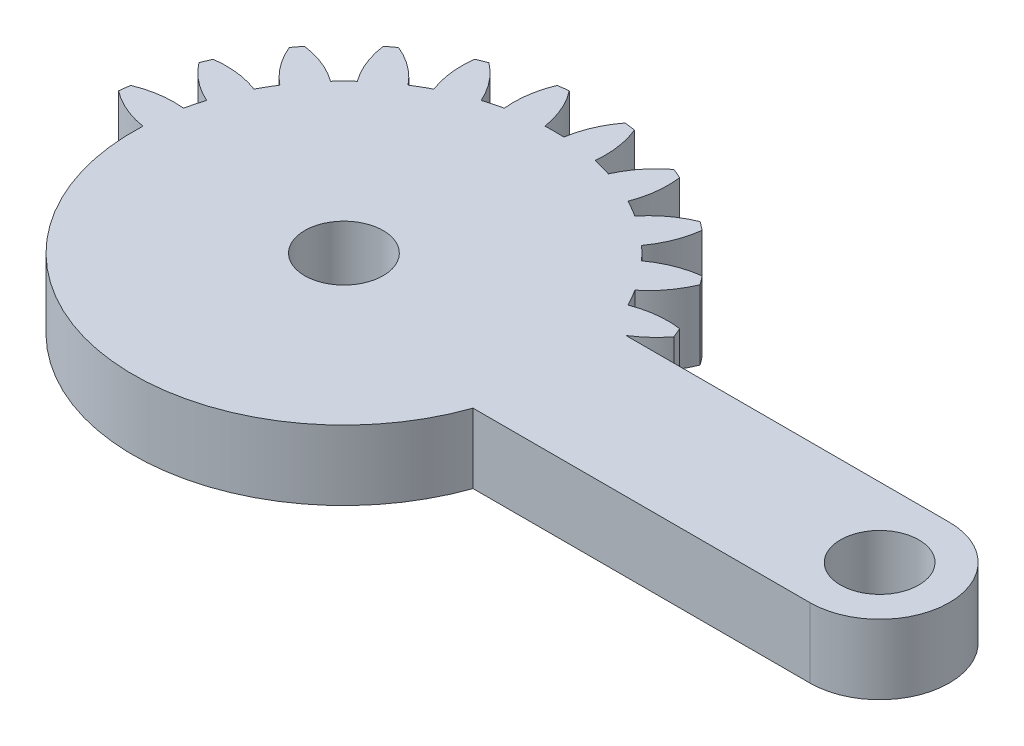
SolidWorks part; units mm, degrees
ref_plane "Front Plane" through (0, 0, 0) normal (0, 0, 1) x (1, 0, 0)
ref_plane "Top Plane" through (0, 0, 0) normal (0, 1, 0) x (1, 0, 0)
ref_plane "Right Plane" through (0, 0, 0) normal (1, 0, 0) x (0, 0, -1)
sketch "Sketch1" plane through (0, 0, 0) normal (0, 1, 0) x (1, 0, 0)
  line L0 (20.6437, 4) -> (2.0816, 4)
  line L1 (2.0816, -4) -> (20.6437, -4)
  arc A0 (2.0816, 4) -> (3.5217, 5.3071) centre (-0.7683, 8.5867) ccw
  arc A1 (3.5217, 5.3071) -> (3.2829, 5.8838) centre (-10.1063, 0) ccw
  arc A2 (3.2829, 5.8838) -> (0.6271, 5.5703) centre (2.5684, 0.5313) ccw
  arc A3 (0.6271, 5.5703) -> (0.0844, 6.5103) centre (-10.1063, 0) ccw
  arc A4 (0.0844, 6.5103) -> (1.6838, 8.6535) centre (-3.3089, 10.711) ccw
  arc A5 (1.6838, 8.6535) -> (1.3038, 9.1487) centre (-10.1063, 0) ccw
  arc A6 (1.3038, 9.1487) -> (-1.1803, 8.1585) centre (1.999, 3.7936) ccw
  arc A7 (-1.1803, 8.1585) -> (-1.9479, 8.926) centre (-10.1063, 0) ccw
  arc A8 (-1.9479, 8.926) -> (-0.9576, 11.4102) centre (-6.3127, 12.1053) ccw
  arc A9 (-0.9576, 11.4102) -> (-1.4528, 11.7901) centre (-10.1063, 0) ccw
  arc A10 (-1.4528, 11.7901) -> (-3.596, 10.1907) centre (0.6046, 6.7975) ccw
  arc A11 (-3.596, 10.1907) -> (-4.5361, 10.7334) centre (-10.1063, 0) ccw
  arc A12 (-4.5361, 10.7334) -> (-4.2225, 13.3892) centre (-9.5751, 12.6747) ccw
  arc A13 (-4.2225, 13.3892) -> (-4.7992, 13.6281) centre (-10.1063, 0) ccw
  arc A14 (-4.7992, 13.6281) -> (-6.4554, 11.5285) centre (-1.5196, 9.3381) ccw
  arc A15 (-6.4554, 11.5285) -> (-7.5039, 11.8094) centre (-10.1063, 0) ccw
  arc A16 (-7.5039, 11.8094) -> (-7.8884, 14.4558) centre (-12.8736, 12.3803) ccw
  arc A17 (-7.8884, 14.4558) -> (-8.5072, 14.5373) centre (-10.1063, 0) ccw
  arc A18 (-8.5072, 14.5373) -> (-9.5636, 12.0806) centre (-4.2291, 11.2423) ccw
  arc A19 (-9.5636, 12.0806) -> (-10.6491, 12.0806) centre (-10.1063, 0) ccw
  arc A20 (-10.6491, 12.0806) -> (-11.7054, 14.5373) centre (-15.9836, 11.2423) ccw
  arc A21 (-11.7054, 14.5373) -> (-12.3243, 14.4558) centre (-10.1063, 0) ccw
  arc A22 (-12.3243, 14.4558) -> (-12.7088, 11.8094) centre (-7.3391, 12.3803) ccw
  arc A23 (-12.7088, 11.8094) -> (-13.7573, 11.5285) centre (-10.1063, 0) ccw
  arc A24 (-13.7573, 11.5285) -> (-15.4135, 13.6281) centre (-18.6931, 9.3381) ccw
  arc A25 (-15.4135, 13.6281) -> (-15.9901, 13.3892) centre (-10.1063, 0) ccw
  arc A26 (-15.9901, 13.3892) -> (-15.6766, 10.7334) centre (-10.6376, 12.6747) ccw
  arc A27 (-15.6766, 10.7334) -> (-16.6166, 10.1907) centre (-10.1063, 0) ccw
  arc A28 (-16.6166, 10.1907) -> (-18.7599, 11.7901) centre (-20.8173, 6.7975) ccw
  arc A29 (-18.7599, 11.7901) -> (-19.255, 11.4102) centre (-10.1063, 0) ccw
  arc A30 (-19.255, 11.4102) -> (-18.2648, 8.926) centre (-13.9, 12.1053) ccw
  arc A31 (-18.2648, 8.926) -> (-19.0324, 8.1585) centre (-10.1063, 0) ccw
  arc A32 (-19.0324, 8.1585) -> (-21.5165, 9.1487) centre (-22.2117, 3.7936) ccw
  arc A33 (-21.5165, 9.1487) -> (-21.8965, 8.6535) centre (-10.1063, 0) ccw
  arc A34 (-21.8965, 8.6535) -> (-20.2971, 6.5103) centre (-16.9038, 10.711) ccw
  arc A35 (-20.2971, 6.5103) -> (-20.8398, 5.5703) centre (-10.1063, 0) ccw
  arc A36 (-20.8398, 5.5703) -> (-23.4956, 5.8838) centre (-22.7811, 0.5313) ccw
  arc A37 (-23.4956, 5.8838) -> (-23.7344, 5.3071) centre (-10.1063, 0) ccw
  arc A38 (-23.7344, 5.3071) -> (-21.6348, 3.6509) centre (-19.4444, 8.5867) ccw
  arc A39 (-21.6348, 3.6509) -> (-21.9157, 2.6025) centre (-10.1063, 0) ccw
  arc A40 (-21.9157, 2.6025) -> (-24.5622, 2.2179) centre (-22.4867, -2.7673) ccw
  arc A41 (-24.5622, 2.2179) -> (-24.6437, 1.5991) centre (-10.1063, 0) ccw
  arc A42 (-24.6437, 1.5991) -> (-22.1869, 0.5427) centre (-21.3486, 5.8773) ccw
  arc A43 (-22.1869, 0.5427) -> (-22.1869, -0.5427) centre (-10.1063, 0) ccw
  arc A44 (-22.1869, -0.5427) -> (-24.6437, -1.5991) centre (-21.3486, -5.8773) ccw
  arc A45 (-24.6437, -1.5991) -> (-24.5622, -2.2179) centre (-10.1063, 0) ccw
  arc A46 (-24.5622, -2.2179) -> (-21.9157, -2.6025) centre (-22.4867, 2.7673) ccw
  arc A47 (-21.9157, -2.6025) -> (-21.6348, -3.6509) centre (-10.1063, 0) ccw
  arc A48 (-21.6348, -3.6509) -> (-23.7344, -5.3071) centre (-19.4444, -8.5867) ccw
  arc A49 (-23.7344, -5.3071) -> (-23.4956, -5.8838) centre (-10.1063, 0) ccw
  arc A50 (-23.4956, -5.8838) -> (-20.8398, -5.5703) centre (-22.7811, -0.5313) ccw
  arc A51 (-20.8398, -5.5703) -> (-20.2971, -6.5103) centre (-10.1063, 0) ccw
  arc A52 (-20.2971, -6.5103) -> (-21.8965, -8.6535) centre (-16.9038, -10.711) ccw
  arc A53 (-21.8965, -8.6535) -> (-21.5165, -9.1487) centre (-10.1063, 0) ccw
  arc A54 (-21.5165, -9.1487) -> (-19.0324, -8.1585) centre (-22.2117, -3.7936) ccw
  arc A55 (-19.0324, -8.1585) -> (-18.2648, -8.926) centre (-10.1063, 0) ccw
  arc A56 (-18.2648, -8.926) -> (-19.255, -11.4102) centre (-13.9, -12.1053) ccw
  arc A57 (-19.255, -11.4102) -> (-18.7599, -11.7901) centre (-10.1063, 0) ccw
  arc A58 (-18.7599, -11.7901) -> (-16.6166, -10.1907) centre (-20.8173, -6.7975) ccw
  arc A59 (-16.6166, -10.1907) -> (-15.6766, -10.7334) centre (-10.1063, 0) ccw
  arc A60 (-15.6766, -10.7334) -> (-15.9901, -13.3892) centre (-10.6376, -12.6747) ccw
  arc A61 (-15.9901, -13.3892) -> (-15.4135, -13.6281) centre (-10.1063, 0) ccw
  arc A62 (-15.4135, -13.6281) -> (-13.7573, -11.5285) centre (-18.6931, -9.3381) ccw
  arc A63 (-13.7573, -11.5285) -> (-12.7088, -11.8094) centre (-10.1063, 0) ccw
  arc A64 (-12.7088, -11.8094) -> (-12.3243, -14.4558) centre (-7.3391, -12.3803) ccw
  arc A65 (-12.3243, -14.4558) -> (-11.7054, -14.5373) centre (-10.1063, 0) ccw
  arc A66 (-11.7054, -14.5373) -> (-10.6491, -12.0806) centre (-15.9836, -11.2423) ccw
  arc A67 (-10.6491, -12.0806) -> (-9.5636, -12.0806) centre (-10.1063, 0) ccw
  arc A68 (-9.5636, -12.0806) -> (-8.5072, -14.5373) centre (-4.2291, -11.2423) ccw
  arc A69 (-8.5072, -14.5373) -> (-7.8884, -14.4558) centre (-10.1063, 0) ccw
  arc A70 (-7.8884, -14.4558) -> (-7.5039, -11.8094) centre (-12.8736, -12.3803) ccw
  arc A71 (-7.5039, -11.8094) -> (-6.4554, -11.5285) centre (-10.1063, 0) ccw
  arc A72 (-6.4554, -11.5285) -> (-4.7992, -13.6281) centre (-1.5196, -9.3381) ccw
  arc A73 (-4.7992, -13.6281) -> (-4.2225, -13.3892) centre (-10.1063, 0) ccw
  arc A74 (-4.2225, -13.3892) -> (-4.5361, -10.7334) centre (-9.5751, -12.6747) ccw
  arc A75 (-4.5361, -10.7334) -> (-3.596, -10.1907) centre (-10.1063, 0) ccw
  arc A76 (-3.596, -10.1907) -> (-1.4528, -11.7901) centre (0.6046, -6.7975) ccw
  arc A77 (-1.4528, -11.7901) -> (-0.9576, -11.4102) centre (-10.1063, 0) ccw
  arc A78 (-0.9576, -11.4102) -> (-1.9479, -8.926) centre (-6.3127, -12.1053) ccw
  arc A79 (-1.9479, -8.926) -> (-1.1803, -8.1585) centre (-10.1063, 0) ccw
  arc A80 (-1.1803, -8.1585) -> (1.3038, -9.1487) centre (1.999, -3.7936) ccw
  arc A81 (1.3038, -9.1487) -> (1.6838, -8.6535) centre (-10.1063, 0) ccw
  arc A82 (1.6838, -8.6535) -> (0.0844, -6.5103) centre (-3.3089, -10.711) ccw
  arc A83 (0.0844, -6.5103) -> (0.6271, -5.5703) centre (-10.1063, 0) ccw
  arc A84 (0.6271, -5.5703) -> (3.2829, -5.8838) centre (2.5684, -0.5313) ccw
  arc A85 (3.2829, -5.8838) -> (3.5217, -5.3071) centre (-10.1063, 0) ccw
  arc A86 (3.5217, -5.3071) -> (2.0816, -4) centre (-0.7683, -8.5867) ccw
  arc A87 (20.6437, -4) -> (20.6437, 4) centre (20.6437, 0) ccw
  circle A88 centre (-10.1063, 0) radius 2.25
  circle A89 centre (20.6437, 0) radius 2.25
  dimension "D1" = 4.5
  dimension "D2" = 4.5
extrude "Boss-Extrude1" add sketch "Sketch1" along normal blind 4
sketch "Sketch2" plane through (0, 4, 0) normal (0, 1, 0) x (1, 0, 0)
  line L0 (2.0816, -4) -> (1.3057, -4)
  line L2 (20.6437, 4) -> (2.0816, 4)
  line L3 (2.0816, -4) -> (20.6437, -4)
  line L4 (20.6437, 4) -> (2.0816, 4)
  line L5 (2.0816, -4) -> (20.6437, -4)
  circle A0 centre (-10.1063, 0) radius 12.0927
  arc A88 (20.6437, -4) -> (20.6437, 4) centre (20.6437, 0) ccw
  arc A89 (2.0816, 4) -> (3.5217, 5.3071) centre (-0.7683, 8.5867) ccw
  arc A90 (3.5217, 5.3071) -> (3.2829, 5.8838) centre (-10.1063, 0) ccw
  arc A91 (3.2829, 5.8838) -> (0.6271, 5.5703) centre (2.5684, 0.5313) ccw
  arc A92 (0.6271, 5.5703) -> (0.0844, 6.5103) centre (-10.1063, 0) ccw
  arc A93 (0.0844, 6.5103) -> (1.6838, 8.6535) centre (-3.3089, 10.711) ccw
  arc A94 (1.6838, 8.6535) -> (1.3038, 9.1487) centre (-10.1063, 0) ccw
  arc A95 (1.3038, 9.1487) -> (-1.1803, 8.1585) centre (1.999, 3.7936) ccw
  arc A96 (-1.1803, 8.1585) -> (-1.9479, 8.926) centre (-10.1063, 0) ccw
  arc A97 (-1.9479, 8.926) -> (-0.9576, 11.4102) centre (-6.3127, 12.1053) ccw
  arc A98 (-0.9576, 11.4102) -> (-1.4528, 11.7901) centre (-10.1063, 0) ccw
  arc A99 (-1.4528, 11.7901) -> (-3.596, 10.1907) centre (0.6046, 6.7975) ccw
  arc A100 (-3.596, 10.1907) -> (-4.5361, 10.7334) centre (-10.1063, 0) ccw
  arc A101 (-4.5361, 10.7334) -> (-4.2225, 13.3892) centre (-9.5751, 12.6747) ccw
  arc A102 (-4.2225, 13.3892) -> (-4.7992, 13.6281) centre (-10.1063, 0) ccw
  arc A103 (-4.7992, 13.6281) -> (-6.4554, 11.5285) centre (-1.5196, 9.3381) ccw
  arc A104 (-6.4554, 11.5285) -> (-7.5039, 11.8094) centre (-10.1063, 0) ccw
  arc A105 (-7.5039, 11.8094) -> (-7.8884, 14.4558) centre (-12.8736, 12.3803) ccw
  arc A106 (-7.8884, 14.4558) -> (-8.5072, 14.5373) centre (-10.1063, 0) ccw
  arc A107 (-8.5072, 14.5373) -> (-9.5636, 12.0806) centre (-4.2291, 11.2423) ccw
  arc A108 (-9.5636, 12.0806) -> (-10.6491, 12.0806) centre (-10.1063, 0) ccw
  arc A109 (-10.6491, 12.0806) -> (-11.7054, 14.5373) centre (-15.9836, 11.2423) ccw
  arc A110 (-11.7054, 14.5373) -> (-12.3243, 14.4558) centre (-10.1063, 0) ccw
  arc A111 (-12.3243, 14.4558) -> (-12.7088, 11.8094) centre (-7.3391, 12.3803) ccw
  arc A112 (-12.7088, 11.8094) -> (-13.7573, 11.5285) centre (-10.1063, 0) ccw
  arc A113 (-13.7573, 11.5285) -> (-15.4135, 13.6281) centre (-18.6931, 9.3381) ccw
  arc A114 (-15.4135, 13.6281) -> (-15.9901, 13.3892) centre (-10.1063, 0) ccw
  arc A115 (-15.9901, 13.3892) -> (-15.6766, 10.7334) centre (-10.6376, 12.6747) ccw
  arc A116 (-15.6766, 10.7334) -> (-16.6166, 10.1907) centre (-10.1063, 0) ccw
  arc A117 (-16.6166, 10.1907) -> (-18.7599, 11.7901) centre (-20.8173, 6.7975) ccw
  arc A118 (-18.7599, 11.7901) -> (-19.255, 11.4102) centre (-10.1063, 0) ccw
  arc A119 (-19.255, 11.4102) -> (-18.2648, 8.926) centre (-13.9, 12.1053) ccw
  arc A120 (-18.2648, 8.926) -> (-19.0324, 8.1585) centre (-10.1063, 0) ccw
  arc A121 (-19.0324, 8.1585) -> (-21.5165, 9.1487) centre (-22.2117, 3.7936) ccw
  arc A122 (-21.5165, 9.1487) -> (-21.8965, 8.6535) centre (-10.1063, 0) ccw
  arc A123 (-21.8965, 8.6535) -> (-20.2971, 6.5103) centre (-16.9038, 10.711) ccw
  arc A124 (-20.2971, 6.5103) -> (-20.8398, 5.5703) centre (-10.1063, 0) ccw
  arc A125 (-20.8398, 5.5703) -> (-23.4956, 5.8838) centre (-22.7811, 0.5313) ccw
  arc A126 (-23.4956, 5.8838) -> (-23.7344, 5.3071) centre (-10.1063, 0) ccw
  arc A127 (-23.7344, 5.3071) -> (-21.6348, 3.6509) centre (-19.4444, 8.5867) ccw
  arc A128 (-21.6348, 3.6509) -> (-21.9157, 2.6025) centre (-10.1063, 0) ccw
  arc A129 (-21.9157, 2.6025) -> (-24.5622, 2.2179) centre (-22.4867, -2.7673) ccw
  arc A130 (-24.5622, 2.2179) -> (-24.6437, 1.5991) centre (-10.1063, 0) ccw
  arc A131 (-24.6437, 1.5991) -> (-22.1869, 0.5427) centre (-21.3486, 5.8773) ccw
  arc A132 (-22.1869, 0.5427) -> (-22.1869, -0.5427) centre (-10.1063, 0) ccw
  arc A133 (-22.1869, -0.5427) -> (-24.6437, -1.5991) centre (-21.3486, -5.8773) ccw
  arc A134 (-24.6437, -1.5991) -> (-24.5622, -2.2179) centre (-10.1063, 0) ccw
  arc A135 (-24.5622, -2.2179) -> (-21.9157, -2.6025) centre (-22.4867, 2.7673) ccw
  arc A136 (-21.9157, -2.6025) -> (-21.6348, -3.6509) centre (-10.1063, 0) ccw
  arc A137 (-21.6348, -3.6509) -> (-23.7344, -5.3071) centre (-19.4444, -8.5867) ccw
  arc A138 (-23.7344, -5.3071) -> (-23.4956, -5.8838) centre (-10.1063, 0) ccw
  arc A139 (-23.4956, -5.8838) -> (-20.8398, -5.5703) centre (-22.7811, -0.5313) ccw
  arc A140 (-20.8398, -5.5703) -> (-20.2971, -6.5103) centre (-10.1063, 0) ccw
  arc A141 (-20.2971, -6.5103) -> (-21.8965, -8.6535) centre (-16.9038, -10.711) ccw
  arc A142 (-21.8965, -8.6535) -> (-21.5165, -9.1487) centre (-10.1063, 0) ccw
  arc A143 (-21.5165, -9.1487) -> (-19.0324, -8.1585) centre (-22.2117, -3.7936) ccw
  arc A144 (-19.0324, -8.1585) -> (-18.2648, -8.926) centre (-10.1063, 0) ccw
  arc A145 (-18.2648, -8.926) -> (-19.255, -11.4102) centre (-13.9, -12.1053) ccw
  arc A146 (-19.255, -11.4102) -> (-18.7599, -11.7901) centre (-10.1063, 0) ccw
  arc A147 (-18.7599, -11.7901) -> (-16.6166, -10.1907) centre (-20.8173, -6.7975) ccw
  arc A148 (-16.6166, -10.1907) -> (-15.6766, -10.7334) centre (-10.1063, 0) ccw
  arc A149 (-15.6766, -10.7334) -> (-15.9901, -13.3892) centre (-10.6376, -12.6747) ccw
  arc A150 (-15.9901, -13.3892) -> (-15.4135, -13.6281) centre (-10.1063, 0) ccw
  arc A151 (-15.4135, -13.6281) -> (-13.7573, -11.5285) centre (-18.6931, -9.3381) ccw
  arc A152 (-13.7573, -11.5285) -> (-12.7088, -11.8094) centre (-10.1063, 0) ccw
  arc A153 (-12.7088, -11.8094) -> (-12.3243, -14.4558) centre (-7.3391, -12.3803) ccw
  arc A154 (-12.3243, -14.4558) -> (-11.7054, -14.5373) centre (-10.1063, 0) ccw
  arc A155 (-11.7054, -14.5373) -> (-10.6491, -12.0806) centre (-15.9836, -11.2423) ccw
  arc A156 (-10.6491, -12.0806) -> (-9.5636, -12.0806) centre (-10.1063, 0) ccw
  arc A157 (-9.5636, -12.0806) -> (-8.5072, -14.5373) centre (-4.2291, -11.2423) ccw
  arc A158 (-8.5072, -14.5373) -> (-7.8884, -14.4558) centre (-10.1063, 0) ccw
  arc A159 (-7.8884, -14.4558) -> (-7.5039, -11.8094) centre (-12.8736, -12.3803) ccw
  arc A160 (-7.5039, -11.8094) -> (-6.4554, -11.5285) centre (-10.1063, 0) ccw
  arc A161 (-6.4554, -11.5285) -> (-4.7992, -13.6281) centre (-1.5196, -9.3381) ccw
  arc A162 (-4.7992, -13.6281) -> (-4.2225, -13.3892) centre (-10.1063, 0) ccw
  arc A163 (-4.2225, -13.3892) -> (-4.5361, -10.7334) centre (-9.5751, -12.6747) ccw
  arc A164 (-4.5361, -10.7334) -> (-3.596, -10.1907) centre (-10.1063, 0) ccw
  arc A165 (-3.596, -10.1907) -> (-1.4528, -11.7901) centre (0.6046, -6.7975) ccw
  arc A166 (-1.4528, -11.7901) -> (-0.9576, -11.4102) centre (-10.1063, 0) ccw
  arc A167 (-0.9576, -11.4102) -> (-1.9479, -8.926) centre (-6.3127, -12.1053) ccw
  arc A168 (-1.9479, -8.926) -> (-1.1803, -8.1585) centre (-10.1063, 0) ccw
  arc A169 (-1.1803, -8.1585) -> (1.3038, -9.1487) centre (1.999, -3.7936) ccw
  arc A170 (1.3038, -9.1487) -> (1.6838, -8.6535) centre (-10.1063, 0) ccw
  arc A171 (1.6838, -8.6535) -> (0.0844, -6.5103) centre (-3.3089, -10.711) ccw
  arc A172 (0.0844, -6.5103) -> (0.6271, -5.5703) centre (-10.1063, 0) ccw
  arc A173 (0.6271, -5.5703) -> (3.2829, -5.8838) centre (2.5684, -0.5313) ccw
  arc A174 (3.2829, -5.8838) -> (3.5217, -5.3071) centre (-10.1063, 0) ccw
  arc A175 (3.5217, -5.3071) -> (2.0816, -4) centre (-0.7683, -8.5867) ccw
  arc A176 (20.6437, -4) -> (20.6437, 4) centre (20.6437, 0) ccw
  arc A177 (2.0816, 4) -> (3.5217, 5.3071) centre (-0.7683, 8.5867) ccw
  arc A178 (3.5217, 5.3071) -> (3.2829, 5.8838) centre (-10.1063, 0) ccw
  arc A179 (3.2829, 5.8838) -> (0.6271, 5.5703) centre (2.5684, 0.5313) ccw
  arc A180 (0.6271, 5.5703) -> (0.0844, 6.5103) centre (-10.1063, 0) ccw
  arc A181 (0.0844, 6.5103) -> (1.6838, 8.6535) centre (-3.3089, 10.711) ccw
  arc A182 (1.6838, 8.6535) -> (1.3038, 9.1487) centre (-10.1063, 0) ccw
  arc A183 (1.3038, 9.1487) -> (-1.1803, 8.1585) centre (1.999, 3.7936) ccw
  arc A184 (-1.1803, 8.1585) -> (-1.9479, 8.926) centre (-10.1063, 0) ccw
  arc A185 (-1.9479, 8.926) -> (-0.9576, 11.4102) centre (-6.3127, 12.1053) ccw
  arc A186 (-0.9576, 11.4102) -> (-1.4528, 11.7901) centre (-10.1063, 0) ccw
  arc A187 (-1.4528, 11.7901) -> (-3.596, 10.1907) centre (0.6046, 6.7975) ccw
  arc A188 (-3.596, 10.1907) -> (-4.5361, 10.7334) centre (-10.1063, 0) ccw
  arc A189 (-4.5361, 10.7334) -> (-4.2225, 13.3892) centre (-9.5751, 12.6747) ccw
  arc A190 (-4.2225, 13.3892) -> (-4.7992, 13.6281) centre (-10.1063, 0) ccw
  arc A191 (-4.7992, 13.6281) -> (-6.4554, 11.5285) centre (-1.5196, 9.3381) ccw
  arc A192 (-6.4554, 11.5285) -> (-7.5039, 11.8094) centre (-10.1063, 0) ccw
  arc A193 (-7.5039, 11.8094) -> (-7.8884, 14.4558) centre (-12.8736, 12.3803) ccw
  arc A194 (-7.8884, 14.4558) -> (-8.5072, 14.5373) centre (-10.1063, 0) ccw
  arc A195 (-8.5072, 14.5373) -> (-9.5636, 12.0806) centre (-4.2291, 11.2423) ccw
  arc A196 (-9.5636, 12.0806) -> (-10.6491, 12.0806) centre (-10.1063, 0) ccw
  arc A197 (-10.6491, 12.0806) -> (-11.7054, 14.5373) centre (-15.9836, 11.2423) ccw
  arc A198 (-11.7054, 14.5373) -> (-12.3243, 14.4558) centre (-10.1063, 0) ccw
  arc A199 (-12.3243, 14.4558) -> (-12.7088, 11.8094) centre (-7.3391, 12.3803) ccw
  arc A200 (-12.7088, 11.8094) -> (-13.7573, 11.5285) centre (-10.1063, 0) ccw
  arc A201 (-13.7573, 11.5285) -> (-15.4135, 13.6281) centre (-18.6931, 9.3381) ccw
  arc A202 (-15.4135, 13.6281) -> (-15.9901, 13.3892) centre (-10.1063, 0) ccw
  arc A203 (-15.9901, 13.3892) -> (-15.6766, 10.7334) centre (-10.6376, 12.6747) ccw
  arc A204 (-15.6766, 10.7334) -> (-16.6166, 10.1907) centre (-10.1063, 0) ccw
  arc A205 (-16.6166, 10.1907) -> (-18.7599, 11.7901) centre (-20.8173, 6.7975) ccw
  arc A206 (-18.7599, 11.7901) -> (-19.255, 11.4102) centre (-10.1063, 0) ccw
  arc A207 (-19.255, 11.4102) -> (-18.2648, 8.926) centre (-13.9, 12.1053) ccw
  arc A208 (-18.2648, 8.926) -> (-19.0324, 8.1585) centre (-10.1063, 0) ccw
  arc A209 (-19.0324, 8.1585) -> (-21.5165, 9.1487) centre (-22.2117, 3.7936) ccw
  arc A210 (-21.5165, 9.1487) -> (-21.8965, 8.6535) centre (-10.1063, 0) ccw
  arc A211 (-21.8965, 8.6535) -> (-20.2971, 6.5103) centre (-16.9038, 10.711) ccw
  arc A212 (-20.2971, 6.5103) -> (-20.8398, 5.5703) centre (-10.1063, 0) ccw
  arc A213 (-20.8398, 5.5703) -> (-23.4956, 5.8838) centre (-22.7811, 0.5313) ccw
  arc A214 (-23.4956, 5.8838) -> (-23.7344, 5.3071) centre (-10.1063, 0) ccw
  arc A215 (-23.7344, 5.3071) -> (-21.6348, 3.6509) centre (-19.4444, 8.5867) ccw
  arc A216 (-21.6348, 3.6509) -> (-21.9157, 2.6025) centre (-10.1063, 0) ccw
  arc A217 (-21.9157, 2.6025) -> (-24.5622, 2.2179) centre (-22.4867, -2.7673) ccw
  arc A218 (-24.5622, 2.2179) -> (-24.6437, 1.5991) centre (-10.1063, 0) ccw
  arc A219 (-24.6437, 1.5991) -> (-22.1869, 0.5427) centre (-21.3486, 5.8773) ccw
  arc A220 (-22.1869, 0.5427) -> (-22.1869, -0.5427) centre (-10.1063, 0) ccw
  arc A221 (-22.1869, -0.5427) -> (-24.6437, -1.5991) centre (-21.3486, -5.8773) ccw
  arc A222 (-24.6437, -1.5991) -> (-24.5622, -2.2179) centre (-10.1063, 0) ccw
  arc A223 (-24.5622, -2.2179) -> (-21.9157, -2.6025) centre (-22.4867, 2.7673) ccw
  arc A224 (-21.9157, -2.6025) -> (-21.6348, -3.6509) centre (-10.1063, 0) ccw
  arc A225 (-21.6348, -3.6509) -> (-23.7344, -5.3071) centre (-19.4444, -8.5867) ccw
  arc A226 (-23.7344, -5.3071) -> (-23.4956, -5.8838) centre (-10.1063, 0) ccw
  arc A227 (-23.4956, -5.8838) -> (-20.8398, -5.5703) centre (-22.7811, -0.5313) ccw
  arc A228 (-20.8398, -5.5703) -> (-20.2971, -6.5103) centre (-10.1063, 0) ccw
  arc A229 (-20.2971, -6.5103) -> (-21.8965, -8.6535) centre (-16.9038, -10.711) ccw
  arc A230 (-21.8965, -8.6535) -> (-21.5165, -9.1487) centre (-10.1063, 0) ccw
  arc A231 (-21.5165, -9.1487) -> (-19.0324, -8.1585) centre (-22.2117, -3.7936) ccw
  arc A232 (-19.0324, -8.1585) -> (-18.2648, -8.926) centre (-10.1063, 0) ccw
  arc A233 (-18.2648, -8.926) -> (-19.255, -11.4102) centre (-13.9, -12.1053) ccw
  arc A234 (-19.255, -11.4102) -> (-18.7599, -11.7901) centre (-10.1063, 0) ccw
  arc A235 (-18.7599, -11.7901) -> (-16.6166, -10.1907) centre (-20.8173, -6.7975) ccw
  arc A236 (-16.6166, -10.1907) -> (-15.6766, -10.7334) centre (-10.1063, 0) ccw
  arc A237 (-15.6766, -10.7334) -> (-15.9901, -13.3892) centre (-10.6376, -12.6747) ccw
  arc A238 (-15.9901, -13.3892) -> (-15.4135, -13.6281) centre (-10.1063, 0) ccw
  arc A239 (-15.4135, -13.6281) -> (-13.7573, -11.5285) centre (-18.6931, -9.3381) ccw
  arc A240 (-13.7573, -11.5285) -> (-12.7088, -11.8094) centre (-10.1063, 0) ccw
  arc A241 (-12.7088, -11.8094) -> (-12.3243, -14.4558) centre (-7.3391, -12.3803) ccw
  arc A242 (-12.3243, -14.4558) -> (-11.7054, -14.5373) centre (-10.1063, 0) ccw
  arc A243 (-11.7054, -14.5373) -> (-10.6491, -12.0806) centre (-15.9836, -11.2423) ccw
  arc A244 (-10.6491, -12.0806) -> (-9.5636, -12.0806) centre (-10.1063, 0) ccw
  arc A245 (-9.5636, -12.0806) -> (-8.5072, -14.5373) centre (-4.2291, -11.2423) ccw
  arc A246 (-8.5072, -14.5373) -> (-7.8884, -14.4558) centre (-10.1063, 0) ccw
  arc A247 (-7.8884, -14.4558) -> (-7.5039, -11.8094) centre (-12.8736, -12.3803) ccw
  arc A248 (-7.5039, -11.8094) -> (-6.4554, -11.5285) centre (-10.1063, 0) ccw
  arc A249 (-6.4554, -11.5285) -> (-4.7992, -13.6281) centre (-1.5196, -9.3381) ccw
  arc A250 (-4.7992, -13.6281) -> (-4.2225, -13.3892) centre (-10.1063, 0) ccw
  arc A251 (-4.2225, -13.3892) -> (-4.5361, -10.7334) centre (-9.5751, -12.6747) ccw
  arc A252 (-4.5361, -10.7334) -> (-3.596, -10.1907) centre (-10.1063, 0) ccw
  arc A253 (-3.596, -10.1907) -> (-1.4528, -11.7901) centre (0.6046, -6.7975) ccw
  arc A254 (-1.4528, -11.7901) -> (-0.9576, -11.4102) centre (-10.1063, 0) ccw
  arc A255 (-0.9576, -11.4102) -> (-1.9479, -8.926) centre (-6.3127, -12.1053) ccw
  arc A256 (-1.9479, -8.926) -> (-1.1803, -8.1585) centre (-10.1063, 0) ccw
  arc A257 (-1.1803, -8.1585) -> (1.3038, -9.1487) centre (1.999, -3.7936) ccw
  arc A258 (1.3038, -9.1487) -> (1.6838, -8.6535) centre (-10.1063, 0) ccw
  arc A259 (1.6838, -8.6535) -> (0.0844, -6.5103) centre (-3.3089, -10.711) ccw
  arc A260 (0.0844, -6.5103) -> (0.6271, -5.5703) centre (-10.1063, 0) ccw
  arc A261 (0.6271, -5.5703) -> (3.2829, -5.8838) centre (2.5684, -0.5313) ccw
  arc A262 (3.2829, -5.8838) -> (3.5217, -5.3071) centre (-10.1063, 0) ccw
  arc A263 (3.5217, -5.3071) -> (2.0816, -4) centre (-0.7683, -8.5867) ccw
  dimension "D1" = 0
extrude "Cut-Extrude1" cut sketch "Sketch2" against normal blind 10 contours A222 A223 A0 A221 | A226 A227 A0 A225 | A230 A231 A0 A229 | A234 A235 A0 A233 | A238 A239 A0 A237 | A242 A243 A0 A241 | A246 A247 A0 A245 | A250 A251 A0 A249 | A254 A255 A0 A253 | A258 A259 A0 A257 | A262 A263 L0 A0 A261
